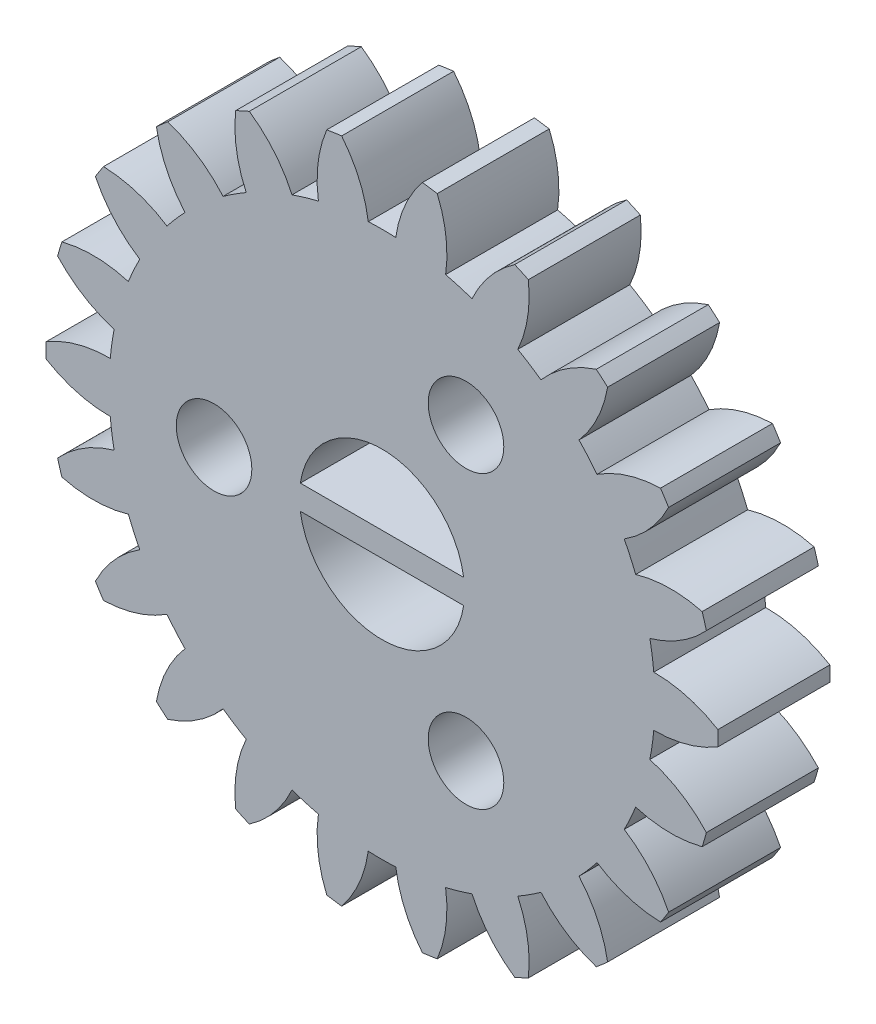
SolidWorks part; units mm, degrees
ref_plane "Front Plane" through (0, 0, 0) normal (0, 0, 1) x (1, 0, 0)
ref_plane "Top Plane" through (0, 0, 0) normal (0, 1, 0) x (1, 0, 0)
ref_plane "Right Plane" through (0, 0, 0) normal (1, 0, 0) x (0, 0, -1)
sketch "Model" plane through (0, 0, 0) normal (0, 0, 1) x (1, 0, 0)
  circle A0 centre (0, 0) radius 2.5
  arc A1 (-11.997, 0.2683) -> (-11.997, -0.2683) centre (0, 0) ccw
  arc A2 (-9.7074, 0.8997) -> (-11.997, 0.2683) centre (-9.7259, -3.5003) ccw
  arc A3 (-9.5676, 1.8717) -> (-9.7074, 0.8997) centre (0, 0) ccw
  arc A4 (-11.5866, 3.1225) -> (-9.5676, 1.8717) centre (-8.3458, 6.0986) ccw
  arc A5 (-11.4355, 3.6374) -> (-11.5866, 3.1225) centre (0, 0) ccw
  arc A6 (-9.0607, 3.5981) -> (-11.4355, 3.6374) centre (-10.3181, -0.6184) ccw
  arc A7 (-8.6528, 4.4914) -> (-9.0607, 3.5981) centre (0, 0) ccw
  arc A8 (-10.2376, 6.2604) -> (-8.6528, 4.4914) centre (-6.2896, 8.2029) ccw
  arc A9 (-9.9475, 6.7118) -> (-10.2376, 6.2604) centre (0, 0) ccw
  arc A10 (-7.68, 6.0051) -> (-9.9475, 6.7118) centre (-10.0744, 2.3136) ccw
  arc A11 (-7.0369, 6.7472) -> (-7.68, 6.0051) centre (0, 0) ccw
  arc A12 (-8.0591, 8.891) -> (-7.0369, 6.7472) centre (-3.7238, 9.6426) ccw
  arc A13 (-7.6536, 9.2424) -> (-8.0591, 8.891) centre (0, 0) ccw
  arc A14 (-5.6771, 7.9255) -> (-7.6536, 9.2424) centre (-9.0145, 5.0582) ccw
  arc A15 (-4.851, 8.4564) -> (-5.6771, 7.9255) centre (0, 0) ccw
  arc A16 (-5.2278, 10.8014) -> (-4.851, 8.4564) centre (-0.8563, 10.3011) ccw
  arc A17 (-4.7397, 11.0243) -> (-5.2278, 10.8014) centre (0, 0) ccw
  arc A18 (-3.2142, 9.2039) -> (-4.7397, 11.0243) centre (-7.2243, 7.3929) ccw
  arc A19 (-2.272, 9.4806) -> (-3.2142, 9.2039) centre (0, 0) ccw
  arc A20 (-1.9729, 11.8367) -> (-2.272, 9.4806) centre (2.0805, 10.1251) ccw
  arc A21 (-1.4418, 11.9131) -> (-1.9729, 11.8367) centre (0, 0) ccw
  arc A22 (-0.491, 9.7366) -> (-1.4418, 11.9131) centre (-4.8488, 9.1288) ccw
  arc A23 (0.491, 9.7366) -> (-0.491, 9.7366) centre (0, 0) ccw
  arc A24 (1.4418, 11.9131) -> (0.491, 9.7366) centre (4.8488, 9.1288) ccw
  arc A25 (1.9729, 11.8367) -> (1.4418, 11.9131) centre (0, 0) ccw
  arc A26 (2.272, 9.4806) -> (1.9729, 11.8367) centre (-2.0805, 10.1251) ccw
  arc A27 (3.2142, 9.2039) -> (2.272, 9.4806) centre (0, 0) ccw
  arc A28 (4.7397, 11.0243) -> (3.2142, 9.2039) centre (7.2243, 7.3929) ccw
  arc A29 (5.2278, 10.8014) -> (4.7397, 11.0243) centre (0, 0) ccw
  arc A30 (4.851, 8.4564) -> (5.2278, 10.8014) centre (0.8563, 10.3011) ccw
  arc A31 (5.6771, 7.9255) -> (4.851, 8.4564) centre (0, 0) ccw
  arc A32 (7.6536, 9.2424) -> (5.6771, 7.9255) centre (9.0145, 5.0582) ccw
  arc A33 (8.0591, 8.891) -> (7.6536, 9.2424) centre (0, 0) ccw
  arc A34 (7.0369, 6.7472) -> (8.0591, 8.891) centre (3.7238, 9.6426) ccw
  arc A35 (7.68, 6.0051) -> (7.0369, 6.7472) centre (0, 0) ccw
  arc A36 (9.9475, 6.7118) -> (7.68, 6.0051) centre (10.0744, 2.3136) ccw
  arc A37 (10.2376, 6.2604) -> (9.9475, 6.7118) centre (0, 0) ccw
  arc A38 (8.6528, 4.4914) -> (10.2376, 6.2604) centre (6.2896, 8.2029) ccw
  arc A39 (9.0607, 3.5981) -> (8.6528, 4.4914) centre (0, 0) ccw
  arc A40 (11.4355, 3.6374) -> (9.0607, 3.5981) centre (10.3181, -0.6184) ccw
  arc A41 (11.5866, 3.1225) -> (11.4355, 3.6374) centre (0, 0) ccw
  arc A42 (9.5676, 1.8717) -> (11.5866, 3.1225) centre (8.3458, 6.0986) ccw
  arc A43 (9.7074, 0.8997) -> (9.5676, 1.8717) centre (0, 0) ccw
  arc A44 (11.997, 0.2683) -> (9.7074, 0.8997) centre (9.7259, -3.5003) ccw
  arc A45 (11.997, -0.2683) -> (11.997, 0.2683) centre (0, 0) ccw
  arc A46 (9.7074, -0.8997) -> (11.997, -0.2683) centre (9.7259, 3.5003) ccw
  arc A47 (9.5676, -1.8717) -> (9.7074, -0.8997) centre (0, 0) ccw
  arc A48 (11.5866, -3.1225) -> (9.5676, -1.8717) centre (8.3458, -6.0986) ccw
  arc A49 (11.4355, -3.6374) -> (11.5866, -3.1225) centre (0, 0) ccw
  arc A50 (9.0607, -3.5981) -> (11.4355, -3.6374) centre (10.3181, 0.6184) ccw
  arc A51 (8.6528, -4.4914) -> (9.0607, -3.5981) centre (0, 0) ccw
  arc A52 (10.2376, -6.2604) -> (8.6528, -4.4914) centre (6.2896, -8.2029) ccw
  arc A53 (9.9475, -6.7118) -> (10.2376, -6.2604) centre (0, 0) ccw
  arc A54 (7.68, -6.0051) -> (9.9475, -6.7118) centre (10.0744, -2.3136) ccw
  arc A55 (7.0369, -6.7472) -> (7.68, -6.0051) centre (0, 0) ccw
  arc A56 (8.0591, -8.891) -> (7.0369, -6.7472) centre (3.7238, -9.6426) ccw
  arc A57 (7.6536, -9.2424) -> (8.0591, -8.891) centre (0, 0) ccw
  arc A58 (5.6771, -7.9255) -> (7.6536, -9.2424) centre (9.0145, -5.0582) ccw
  arc A59 (4.851, -8.4564) -> (5.6771, -7.9255) centre (0, 0) ccw
  arc A60 (5.2278, -10.8014) -> (4.851, -8.4564) centre (0.8563, -10.3011) ccw
  arc A61 (4.7397, -11.0243) -> (5.2278, -10.8014) centre (0, 0) ccw
  arc A62 (3.2142, -9.2039) -> (4.7397, -11.0243) centre (7.2243, -7.3929) ccw
  arc A63 (2.272, -9.4806) -> (3.2142, -9.2039) centre (0, 0) ccw
  arc A64 (1.9729, -11.8367) -> (2.272, -9.4806) centre (-2.0805, -10.1251) ccw
  arc A65 (1.4418, -11.9131) -> (1.9729, -11.8367) centre (0, 0) ccw
  arc A66 (0.491, -9.7366) -> (1.4418, -11.9131) centre (4.8488, -9.1288) ccw
  arc A67 (-0.491, -9.7366) -> (0.491, -9.7366) centre (0, 0) ccw
  arc A68 (-1.4418, -11.9131) -> (-0.491, -9.7366) centre (-4.8488, -9.1288) ccw
  arc A69 (-1.9729, -11.8367) -> (-1.4418, -11.9131) centre (0, 0) ccw
  arc A70 (-2.272, -9.4806) -> (-1.9729, -11.8367) centre (2.0805, -10.1251) ccw
  arc A71 (-3.2142, -9.2039) -> (-2.272, -9.4806) centre (0, 0) ccw
  arc A72 (-4.7397, -11.0243) -> (-3.2142, -9.2039) centre (-7.2243, -7.3929) ccw
  arc A73 (-5.2278, -10.8014) -> (-4.7397, -11.0243) centre (0, 0) ccw
  arc A74 (-4.851, -8.4564) -> (-5.2278, -10.8014) centre (-0.8563, -10.3011) ccw
  arc A75 (-5.6771, -7.9255) -> (-4.851, -8.4564) centre (0, 0) ccw
  arc A76 (-7.6536, -9.2424) -> (-5.6771, -7.9255) centre (-9.0145, -5.0582) ccw
  arc A77 (-8.0591, -8.891) -> (-7.6536, -9.2424) centre (0, 0) ccw
  arc A78 (-7.0369, -6.7472) -> (-8.0591, -8.891) centre (-3.7238, -9.6426) ccw
  arc A79 (-7.68, -6.0051) -> (-7.0369, -6.7472) centre (0, 0) ccw
  arc A80 (-9.9475, -6.7118) -> (-7.68, -6.0051) centre (-10.0744, -2.3136) ccw
  arc A81 (-10.2376, -6.2604) -> (-9.9475, -6.7118) centre (0, 0) ccw
  arc A82 (-8.6528, -4.4914) -> (-10.2376, -6.2604) centre (-6.2896, -8.2029) ccw
  arc A83 (-9.0607, -3.5981) -> (-8.6528, -4.4914) centre (0, 0) ccw
  arc A84 (-11.4355, -3.6374) -> (-9.0607, -3.5981) centre (-10.3181, 0.6184) ccw
  arc A85 (-11.5866, -3.1225) -> (-11.4355, -3.6374) centre (0, 0) ccw
  arc A86 (-9.5676, -1.8717) -> (-11.5866, -3.1225) centre (-8.3458, -6.0986) ccw
  arc A87 (-9.7074, -0.8997) -> (-9.5676, -1.8717) centre (0, 0) ccw
  arc A88 (-11.997, -0.2683) -> (-9.7074, -0.8997) centre (-9.7259, 3.5003) ccw
extrude "Boss-Extrude1" add sketch "Model" along normal blind 4
sketch "Sketch4" plane through (0, 0, 0) normal (0, 0, 1) x (1, 0, 0)
  circle A0 centre (0, 0) radius 11 construction
  dimension "D1" = 22
sketch "Sketch2" plane through (0, 0, 4) normal (0, 0, 1) x (1, 0, 0)
  circle A0 centre (0, 0) radius 2.95
  dimension "D1" = 5.9
extrude "Cut-Extrude1" cut sketch "Sketch2" against normal blind 4
sketch "Sketch3" plane through (0, 0, 4) normal (0, 0, 1) x (1, 0, 0)
  line L0 (0, 0) -> (-9.3925, 0) construction
  line L1 (0, 0) -> (-6, 0) construction
  circle A0 centre (-6, 0) radius 1.35
  dimension "D1" = 2.7
  dimension "D2" = 6
  dimension "D3" = 0
extrude "Cut-Extrude2" cut sketch "Sketch3" against normal blind 4
pattern_circular "CirPattern1" count 3 over 360 about axis through (0, 0, 0) along (0, 0, 1) of "Cut-Extrude2"
sketch "Sketch5" plane through (0, 0, 0) normal (0, 0, 1) x (1, 0, 0)
  line L1 (2.95, 0) -> (-2.95, 0) construction
  line L3 (-3, -0.435) -> (3, -0.435)
  line L4 (-3, -0.435) -> (-3, 0.435)
  line L5 (-3, 0.435) -> (3, 0.435)
  line L6 (3, -0.435) -> (3, 0.435)
  line L7 (0, 0.435) -> (0, -0.435) construction
  line L8 (-3, 0) -> (3, 0) construction
  circle A0 centre (0, 0) radius 2.95 construction
  circle A2 centre (0, 0) radius 2.95
  arc A3 (2.95, 0) -> (-2.95, 0) centre (0, 0) ccw
  dimension "D2" = 0.87
  dimension "D3" = 6
  dimension "D1" = 0
extrude "Boss-Extrude2" add sketch "Sketch5" along normal blind 4
